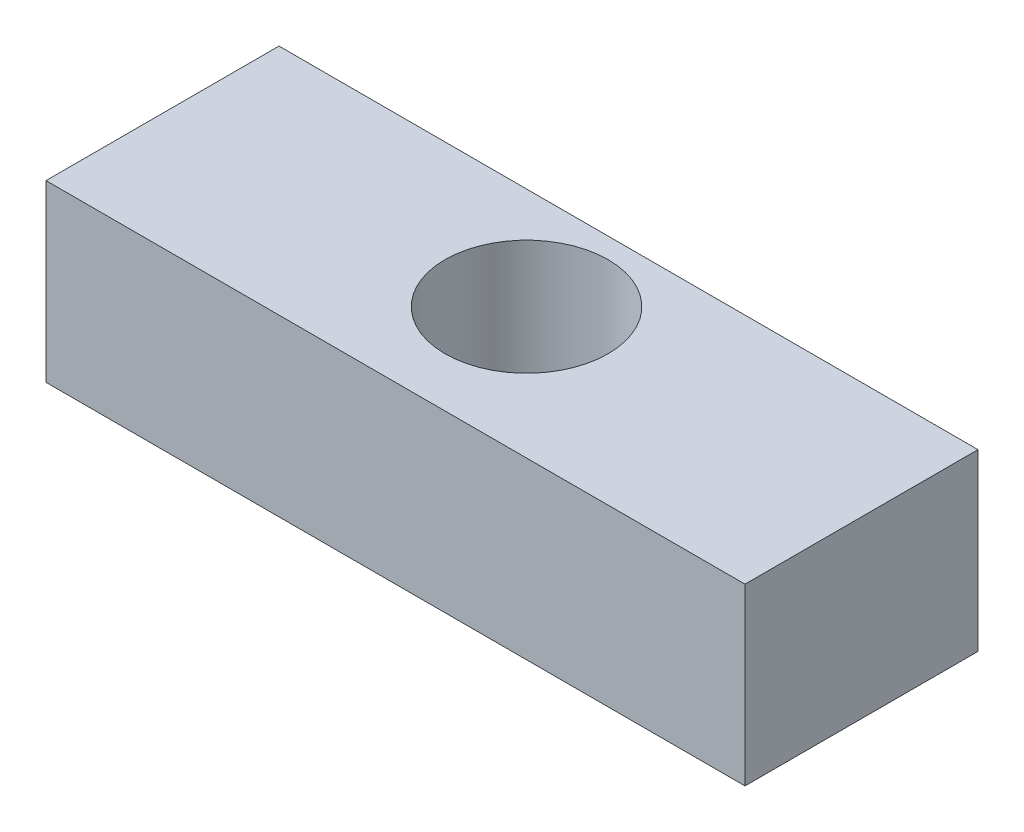
SolidWorks part; units mm, degrees
material "Polyethylene Cross-Linked"
ref_plane "Front Plane" through (0, 0, 0) normal (0, 0, 1) x (1, 0, 0)
ref_plane "Top Plane" through (0, 0, 0) normal (0, 1, 0) x (1, 0, 0)
ref_plane "Right Plane" through (0, 0, 0) normal (1, 0, 0) x (0, 0, -1)
sketch "Sketch1" plane through (0, 0, 0) normal (0, 1, 0) x (1, 0, 0)
  line L1 (0, 0) -> (38.1, 0)
  line L2 (0, 0) -> (0, 12.7)
  line L3 (0, 12.7) -> (38.1, 12.7)
  line L4 (38.1, 0) -> (38.1, 12.7)
  circle A0 centre (19.05, 7.1437) radius 4.445
extrude "Boss-Extrude1" add sketch "Sketch1" along normal blind 9.525
